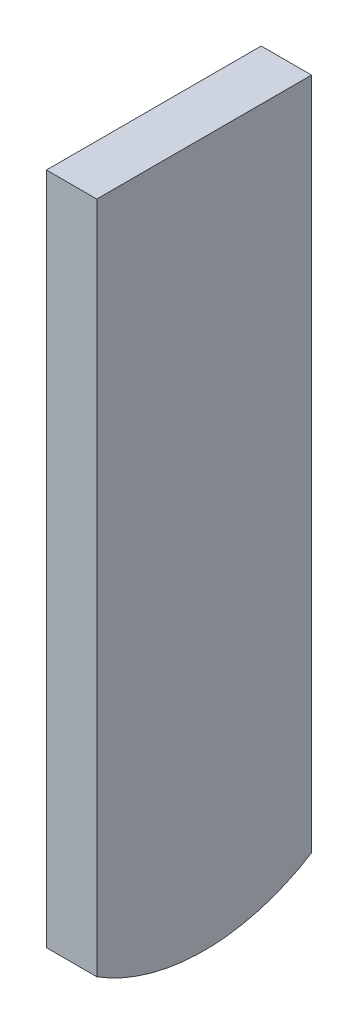
SolidWorks part; units mm, degrees
material "AISI 304"
ref_plane "前视基准面" through (0, 0, 0) normal (0, 0, 1) x (1, 0, 0)
ref_plane "上视基准面" through (0, 0, 0) normal (0, 1, 0) x (1, 0, 0)
ref_plane "右视基准面" through (0, 0, 0) normal (1, 0, 0) x (0, 0, -1)
ref_plane "ConnectFace" through (0, 0, 0) normal (0, 1, 0) x (1, 0, 0)
ref_plane "CenterV" through (0, 0, 0) normal (1, 0, 0) x (0, 0, -1)
ref_plane "CenterH" through (0, 0, 0) normal (0, 0, 1) x (1, 0, 0)
sketch "SPin" plane through (0, 0, 0) normal (0, 1, 0) x (1, 0, 0)
  line L1 (-0.75, -3.2) -> (0.75, -3.2)
  line L2 (-0.75, -3.2) -> (-0.75, 3.2)
  line L3 (-0.75, 3.2) -> (0.75, 3.2)
  line L4 (0.75, -3.2) -> (0.75, 3.2)
  line L5 (-0.75, -3.2) -> (0.75, 3.2) construction
  line L6 (-0.75, 3.2) -> (0.75, -3.2) construction
  point P0 (0, 0)
  dimension "b" = 6.4
  dimension "t" = 1.5
extrude "FPin" add sketch "SPin" against normal blind 21
sketch "SPin2" plane through (0, 0, 0) normal (1, 0, 0) x (0, 0, -1)
  line L0 (0, 0) -> (0, -21) construction
  arc A0 (-3.2, -20.0754) -> (3.2, -20.0754) centre (0, -15) ccw
  dimension "R" = 6
  dimension "D1" = 21
  dimension "D2" = 6.4
extrude "FPin2" cut sketch "SPin2" against normal through all and the other way through all flip side to cut
sketch "CircleBase" plane through (0, 0, 0) normal (0, 1, 0) x (1, 0, 0)
  circle A0 centre (0, 0) radius 5
  dimension "D1" = 10
sketch "RectangleBase" plane through (0, 0, 0) normal (0, 1, 0) x (1, 0, 0)
  line L0 (1.75, 4.2) -> (-1.75, 4.2)
  line L1 (-1.75, 4.2) -> (-1.75, -4.2)
  line L2 (-1.75, -4.2) -> (1.75, -4.2)
  line L3 (1.75, -4.2) -> (1.75, 4.2)
  line L4 (-0.75, -3.2) -> (0.75, -3.2)
  line L5 (0.75, -3.2) -> (0.75, 3.2)
  line L6 (0.75, 3.2) -> (-0.75, 3.2)
  line L7 (-0.75, 3.2) -> (-0.75, -3.2)
  line L8 (-0.75, -3.2) -> (0.75, -3.2) construction
  line L9 (0.75, -3.2) -> (0.75, 3.2) construction
  line L10 (0.75, 3.2) -> (-0.75, 3.2) construction
  line L11 (-0.75, 3.2) -> (-0.75, -3.2) construction
  dimension "D1" = 0
  dimension "D2" = 1
equation "\"D1@SPin2\"=\"L@FPin\""
equation "\"D2@SPin2\"=\"b@SPin\""
